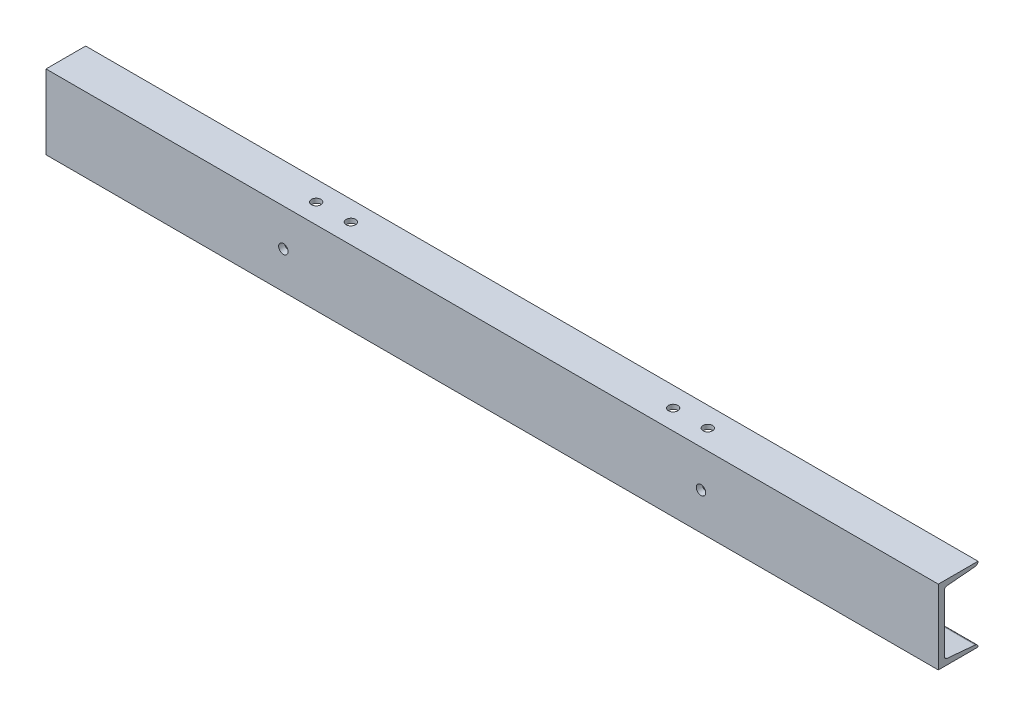
SolidWorks part; units mm, degrees
material "Plain Carbon Steel"
ref_plane "Front Plane" through (0, 0, 0) normal (0, 0, 1) x (1, 0, 0)
ref_plane "Top Plane" through (0, 0, 0) normal (0, 1, 0) x (1, 0, 0)
ref_plane "Right Plane" through (0, 0, 0) normal (1, 0, 0) x (0, 0, -1)
sketch "Sketch1" plane through (0, 0, 0) normal (0, 1, 0) x (1, 0, 0)
  line L0 (-450, 0) -> (450, 0)
  dimension "D1" = 900
other "Structural Member1"
ref_plane "Plane1" through (-450, 0, 0) normal (1, 0, 0) x (0, 0, 1)
sketch "Sketch18" plane through (-450, 0, 0) normal (1, 0, 0) x (0, 0, 1)
  line L0 (0, 37.5) -> (0, -37.5)
  line L1 (0, 37.5) -> (-40, 37.5)
  line L2 (0, -37.5) -> (-40, -37.5)
  line L3 (-6, 28.7531) -> (-6, -28.7531)
  line L4 (-8.7363, 31.7414) -> (-37.2637, 34.2586)
  line L5 (0, 0) -> (-48.9646, 0) construction
  line L6 (-40, 37.2469) -> (-40, 37.5)
  line L7 (-8.7363, -31.7414) -> (-37.2637, -34.2586)
  line L8 (-40, -37.2469) -> (-40, -37.5)
  arc A0 (-6, 28.7531) -> (-8.7363, 31.7414) centre (-9, 28.7531) ccw
  arc A1 (-37.2637, 34.2586) -> (-40, 37.2469) centre (-37, 37.2469) cw
  arc A2 (-6, -28.7531) -> (-8.7363, -31.7414) centre (-9, -28.7531) cw
  arc A3 (-37.2637, -34.2586) -> (-40, -37.2469) centre (-37, -37.2469) ccw
  point P6 (0, 0)
  point P12 (-6, 31.5)
  point P15 (-40, 34.5)
  dimension "D6" = 3
  dimension "D1" = 75
  dimension "D2" = 40
  dimension "D3" = 6
  dimension "D4" = 3
  dimension "D5" = 6
sketch "Sketch12" plane through (0, 0, 0) normal (0, 1, 0) x (1, 0, 0)
  line L0 (-412.5239, 20) -> (413.742, 20) construction
  line L1 (-450, 0) -> (450, 0) construction
  line L2 (0, 0) -> (0, 45.9021) construction
  line L4 (-450, 40) -> (-450, 0) construction
  circle A0 centre (-425, 20) radius 4.7625
  circle A1 centre (425, 20) radius 4.7625
  dimension "D2" = 9.525
  dimension "D1" = 20
  dimension "D3" = 25
extrude "Cut-Extrude1" cut sketch "Sketch12" against normal through all
sketch "Sketch15" plane through (0, 0, -6) normal (0, 0, -1) x (-1, 0, 0)
  line L0 (-425, 105.8991) -> (-425, -40.4286) construction
  line L1 (-375.1366, 27.5) -> (-474.8634, 27.5) construction
  line L2 (-450, 37.5) -> (450, 37.5) construction
  line L3 (-412.5, 27.5) -> (-437.5, 27.5) construction
  line L4 (-412.5, 22.5) -> (-437.5, 22.5)
  line L5 (-412.5, 32.5) -> (-437.5, 32.5)
  line L6 (0, 0) -> (0, -58.1771) construction
  line L7 (412.5, 27.5) -> (437.5, 27.5) construction
  line L8 (412.5, 22.5) -> (437.5, 22.5)
  line L9 (412.5, 32.5) -> (437.5, 32.5)
  arc A0 (-412.5, 22.5) -> (-412.5, 32.5) centre (-412.5, 27.5) ccw
  arc A1 (-437.5, 32.5) -> (-437.5, 22.5) centre (-437.5, 27.5) ccw
  arc A2 (412.5, 22.5) -> (412.5, 32.5) centre (412.5, 27.5) cw
  arc A3 (437.5, 32.5) -> (437.5, 22.5) centre (437.5, 27.5) cw
  ellipse E0 centre (-425, 32.7353) end of major axis (-429.7625, 32.7353) minor radius 0.4202 construction
  point P0 (-425, 32.7353)
  point P11 (-425, 27.5)
  point P16 (-425, 27.5)
  point P26 (425, 27.5)
  dimension "D2" = 5
  dimension "D1" = 10
  dimension "D3" = 25
extrude "Cut-Extrude2" cut sketch "Sketch15" along normal blind 40
sketch "Sketch16" plane through (0, 0, 0) normal (0, 1, 0) x (1, 0, 0)
  line L0 (0, -46.4014) -> (0, 86.4014) construction
  line L1 (-394.0256, 20) -> (394.0256, 20) construction
  circle A0 centre (-197.5, 20) radius 4.7625
  circle A1 centre (-162.5, 20) radius 4.7625
  circle A2 centre (162.5, 20) radius 4.7625
  circle A3 centre (197.5, 20) radius 4.7625
  point P5 (0, 20)
  point P6 (0, 20)
  dimension "D2" = 9.525
  dimension "D1" = 20
  dimension "D3" = 197.5
  dimension "D4" = 35
extrude "Cut-Extrude3" cut sketch "Sketch16" along normal through all
sketch "Sketch19" plane through (0, 0, 0) normal (0, 0, 1) x (1, 0, 0)
  line L0 (0, 0) -> (0, 24.8959) construction
  line L4 (-450, 37.5) -> (-450, -37.5)
  line L5 (-450, -37.5) -> (450, -37.5)
  line L6 (450, -37.5) -> (450, 37.5)
  line L7 (450, 37.5) -> (-450, 37.5)
  line L8 (-450, 37.5) -> (-450, -37.5)
  line L9 (-450, -37.5) -> (450, -37.5)
  line L10 (450, -37.5) -> (450, 37.5)
  line L11 (450, 37.5) -> (-450, 37.5)
  circle A0 centre (210.6, 0) radius 4.7625
  circle A1 centre (210.6, 0) radius 4.7625 construction
  circle A2 centre (-210.6, 0) radius 4.7625
  dimension "D2" = 9.525
  dimension "D1" = 0
extrude "Cut-Extrude5" cut sketch "Sketch19" against normal through all flip side to cut
